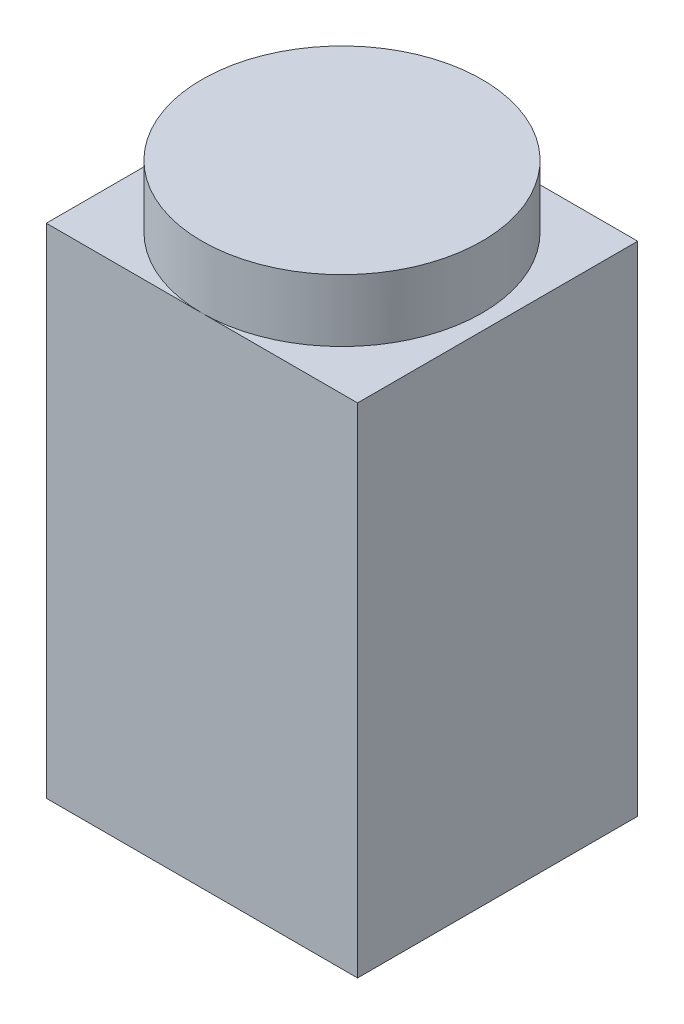
SolidWorks part; units mm, degrees
ref_plane "Front Plane" through (0, 0, 0) normal (0, 0, 1) x (1, 0, 0)
ref_plane "Top Plane" through (0, 0, 0) normal (0, 1, 0) x (1, 0, 0)
ref_plane "Right Plane" through (0, 0, 0) normal (1, 0, 0) x (0, 0, -1)
sketch "Sketch1" plane through (0, 0, 0) normal (0, 1, 0) x (1, 0, 0)
  line L1 (-25, 22.5) -> (25, 22.5)
  line L2 (-25, 22.5) -> (-25, -22.5)
  line L3 (-25, -22.5) -> (25, -22.5)
  line L4 (25, 22.5) -> (25, -22.5)
  point P4 (0, 22.5)
  point P6 (-25, 0)
  dimension "D1" = 45
  dimension "D2" = 50
extrude "Boss-Extrude1" add sketch "Sketch1" along normal mid plane 90
sketch "Sketch2" plane through (0, 45, 0) normal (0, 1, 0) x (1, 0, 0)
  circle A0 centre (0, 0) radius 22.5
extrude "Cut-Extrude1" cut sketch "Sketch2" against normal mid plane 20 flip side to cut
